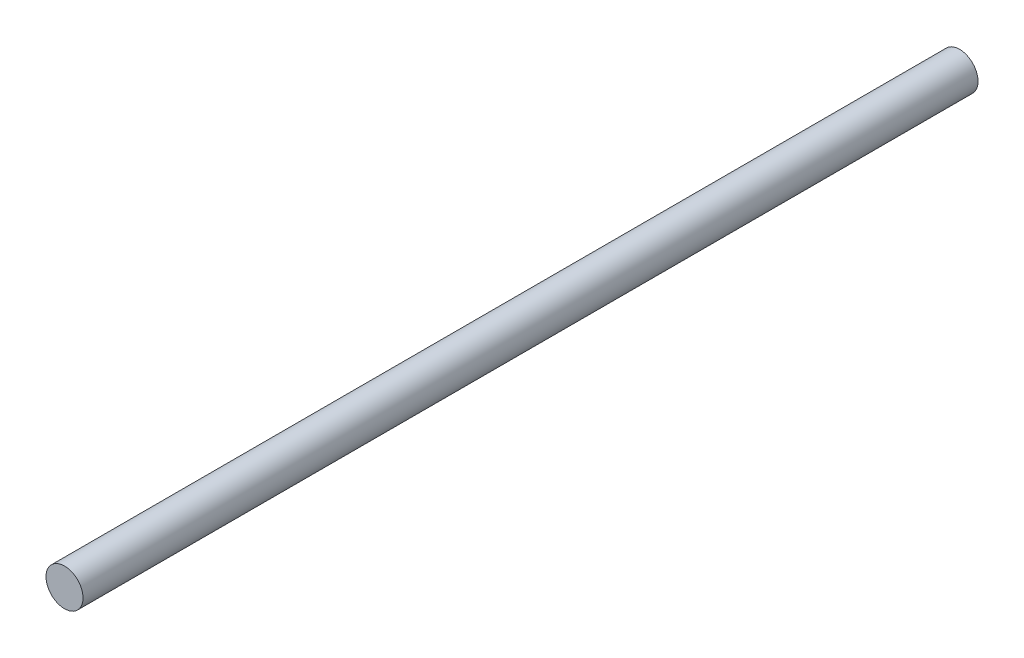
SolidWorks part; units mm, degrees
ref_plane "Front Plane" through (0, 0, 0) normal (0, 0, 1) x (1, 0, 0)
ref_plane "Top Plane" through (0, 0, 0) normal (0, 1, 0) x (1, 0, 0)
ref_plane "Right Plane" through (0, 0, 0) normal (1, 0, 0) x (0, 0, -1)
sketch "Sketch1" plane through (0, 0, 0) normal (0, 0, 1) x (1, 0, 0)
  circle A0 centre (0, 0) radius 6
  dimension "D1" = 12
extrude "Boss-Extrude1" add sketch "Sketch1" along normal blind 250
sketch "Sketch2" plane through (0, 0, 0) normal (0, 0, -1) x (-1, 0, 0)
  circle A0 centre (0, 0) radius 6
  circle A1 centre (0, 0) radius 6 construction
extrude "Boss-Extrude2" add sketch "Sketch2" along normal blind 40
